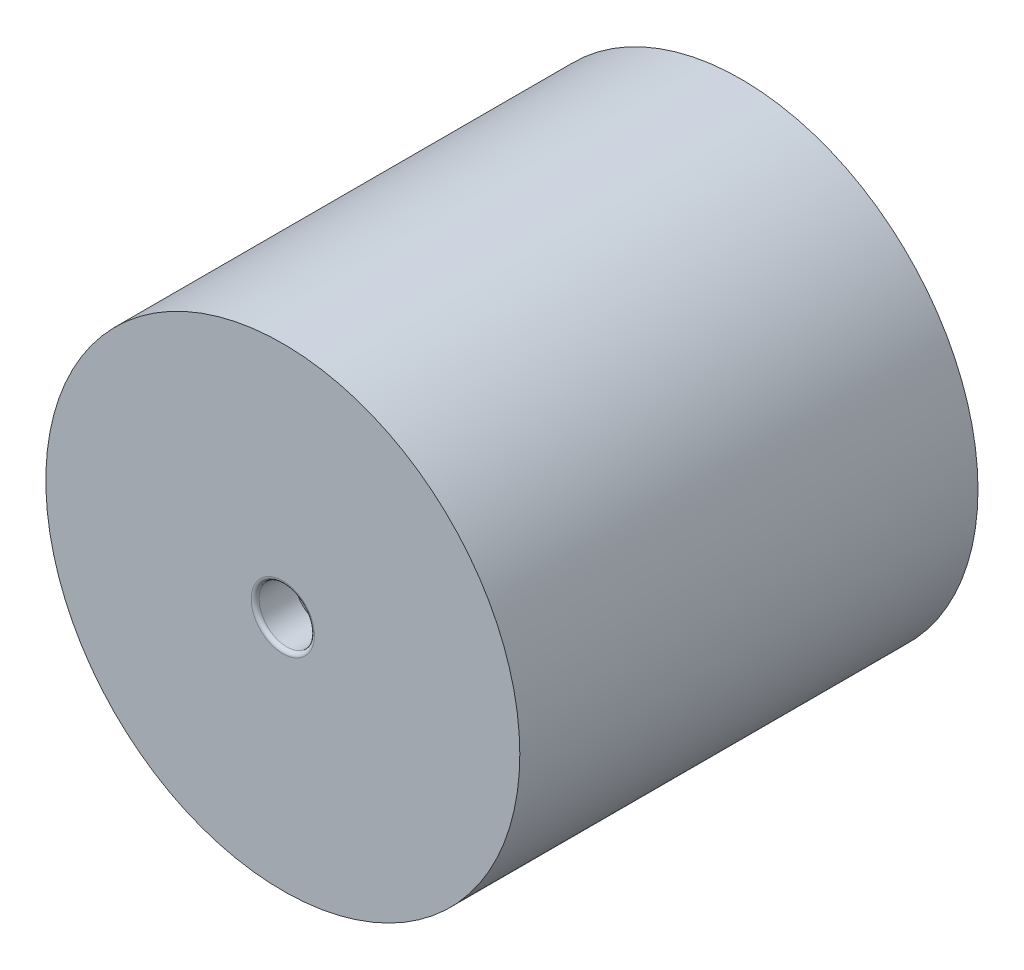
SolidWorks part; units mm, degrees
ref_plane "Front Plane" through (0, 0, 0) normal (0, 0, 1) x (1, 0, 0)
ref_plane "Top Plane" through (0, 0, 0) normal (0, 1, 0) x (1, 0, 0)
ref_plane "Right Plane" through (0, 0, 0) normal (1, 0, 0) x (0, 0, -1)
sketch "Sketch21" plane through (0, 0, 0) normal (0, 0, 1) x (1, 0, 0)
  circle A0 centre (0, 0) radius 30
  dimension "D1" = 60
extrude "Boss-Extrude14" add sketch "Sketch21" along normal mid plane 58
sketch "Sketch24" plane through (0, 0, -29) normal (0, 0, -1) x (-1, 0, 0)
  circle A0 centre (0, 0) radius 3.5
  dimension "D1" = 7
extrude "Cut-Extrude1" cut sketch "Sketch24" against normal blind 5
sketch "Sketch25" plane through (0, 0, 29) normal (0, 0, 1) x (1, 0, 0)
  circle A0 centre (0, 0) radius 3.5
  dimension "D1" = 7
extrude "Cut-Extrude2" cut sketch "Sketch25" against normal blind 5
fillet "Fillet1" radius 0.5 2 edges at (-3.5, 0, -29) (3.5, 0, 29)
